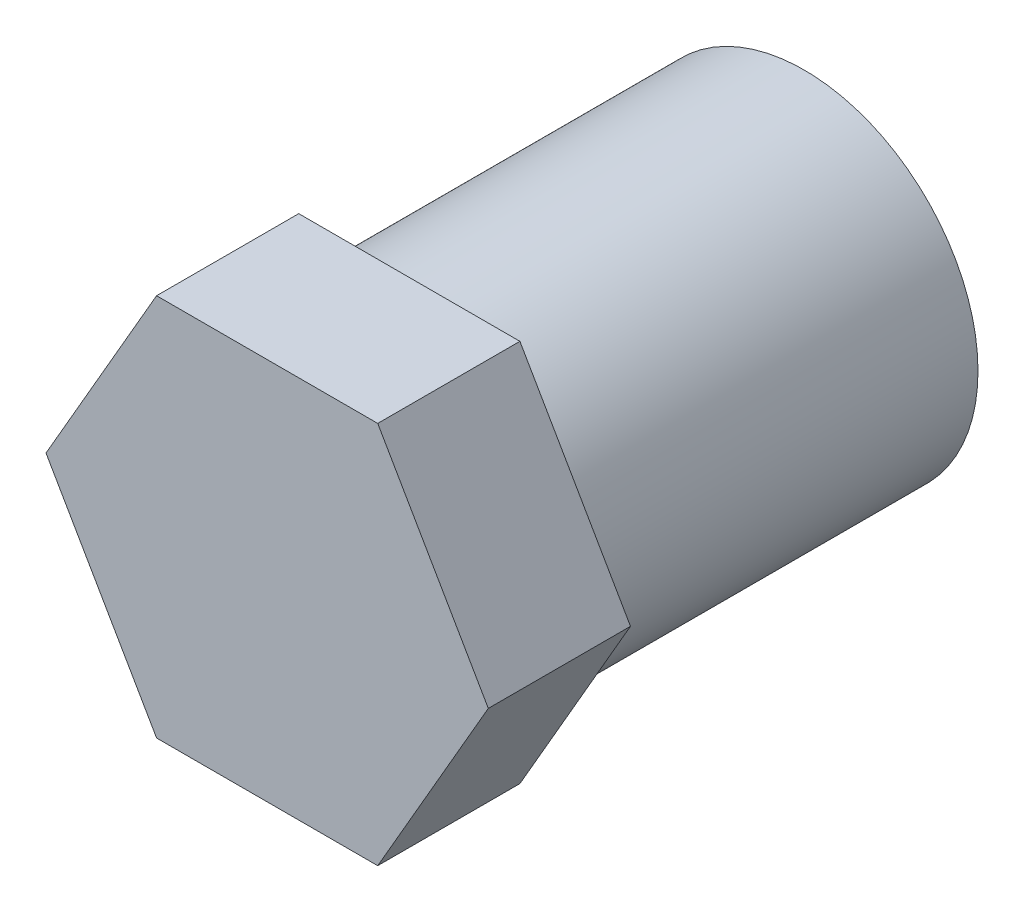
SolidWorks part; units mm, degrees
ref_plane "前视基准面" through (0, 0, 0) normal (0, 0, 1) x (1, 0, 0)
ref_plane "上视基准面" through (0, 0, 0) normal (0, 1, 0) x (1, 0, 0)
ref_plane "右视基准面" through (0, 0, 0) normal (1, 0, 0) x (0, 0, -1)
sketch "草图1" plane through (0, 0, 0) normal (0, 0, 1) x (1, 0, 0)
  circle A0 centre (0, 0) radius 2.5
  circle A1 centre (0, 0) radius 5.5
  dimension "D1" = 5
  dimension "D2" = 11
extrude "凸台-拉伸1" add sketch "草图1" along normal blind 12.5
sketch "草图2" plane through (0, 0, 12.5) normal (0, 0, 1) x (1, 0, 0)
  line L0 (-5.5, 0) -> (5.5, 0) construction
  line L1 (0, 5.5) -> (0, -5.5) construction
  line L2 (-3.5, 6.0622) -> (3.5, 6.0622)
  line L3 (3.5, 6.0622) -> (7, 0)
  line L4 (-3.5, 6.0622) -> (-7, 0)
  line L5 (3.5, -6.0622) -> (7, 0)
  line L6 (-3.5, -6.0622) -> (3.5, -6.0622)
  line L7 (-3.5, -6.0622) -> (-7, 0)
  circle A0 centre (0, 0) radius 5.5 construction
  point P10 (0, 0)
  point P13 (0, 6.0622)
  point P17 (0, 0)
  dimension "D1" = 7
  dimension "D2" = 3.5
  dimension "D3" = 120
extrude "凸台-拉伸2" add sketch "草图2" along normal blind 4.5
